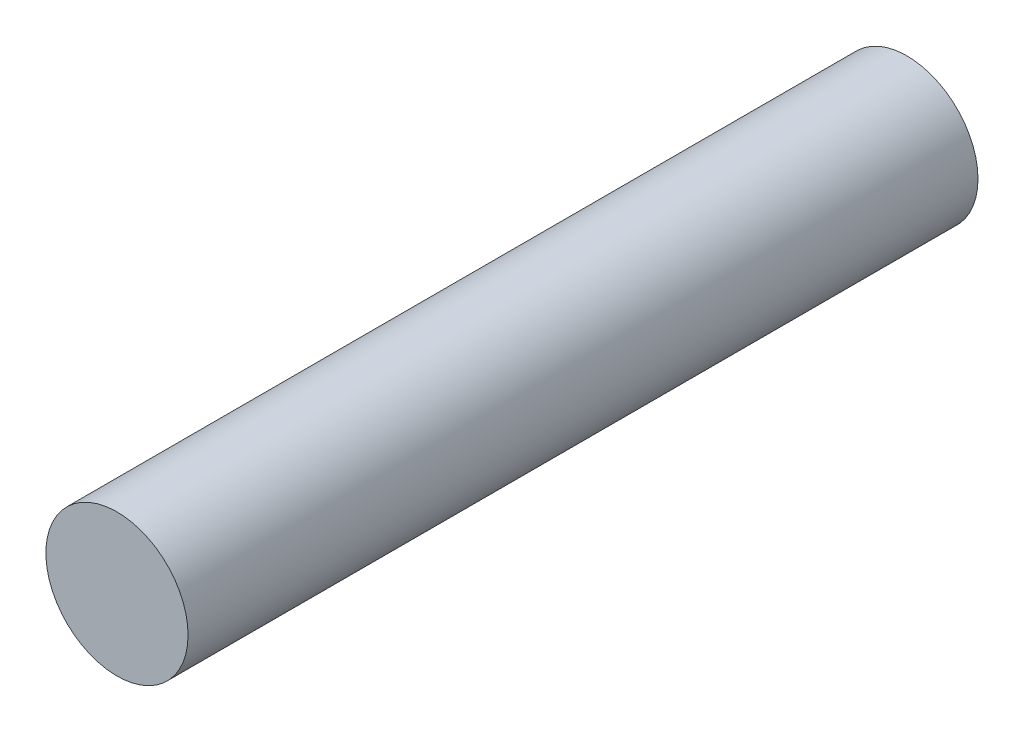
SolidWorks part; units mm, degrees
material "Default"
ref_plane "Top" through (0, 0, 0) normal (0, 0, 1) x (1, 0, 0)
ref_plane "Right" through (0, 0, 0) normal (0, 1, 0) x (1, 0, 0)
ref_plane "Front" through (0, 0, 0) normal (1, 0, 0) x (0, 0, -1)
sketch "Sketch1" plane through (0, 0, 0) normal (0, 0, 1) x (1, 0, 0)
  circle A0 centre (0, 0) radius 1.35
  dimension "D1" = 2.7
extrude "Boss-Extrude1" add sketch "Sketch1" along normal blind 15
